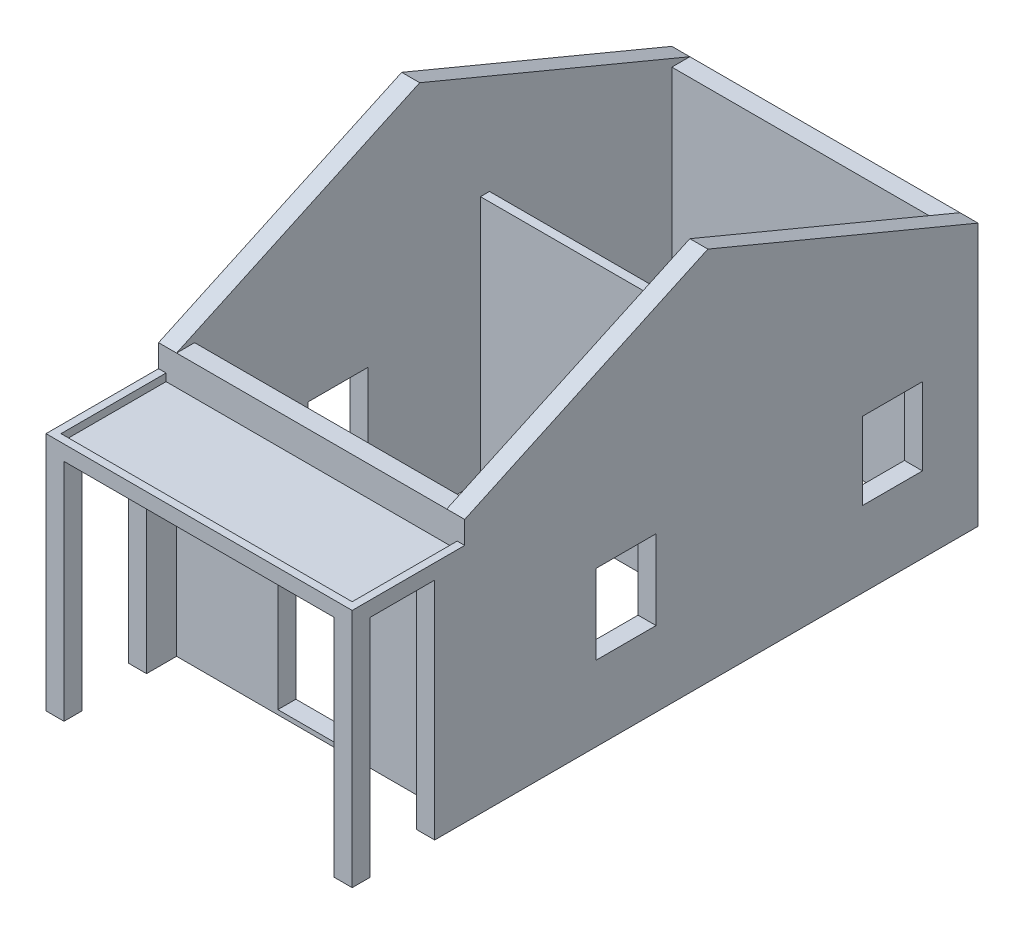
SolidWorks part; units mm, degrees
material "屋面瓦"
ref_plane "前视基准面" through (0, 0, 0) normal (0, 0, 1) x (1, 0, 0)
ref_plane "上视基准面" through (0, 0, 0) normal (0, 1, 0) x (1, 0, 0)
ref_plane "右视基准面" through (0, 0, 0) normal (1, 0, 0) x (0, 0, -1)
sketch "草图1" plane through (0, 0, 0) normal (0, 1, 0) x (1, 0, 0)
  line L1 (0, 0) -> (-3600, 0)
  line L2 (0, 0) -> (0, 6360)
  line L3 (0, 6360) -> (-3600, 6360)
  line L4 (-3600, 0) -> (-3600, 6360)
  point P4 (-1800, 0)
  dimension "D1" = 6360
  dimension "D2" = 3600
extrude "墙" add sketch "草图1" along normal blind 3500 thin thin type one direction wall 240
ref_plane "中间面-宽向" through (-1800, 0, 0) normal (1, 0, 0) x (0, 0, -1)
sketch "草图14" plane through (240, 0, 0) normal (1, 0, 0) x (0, 0, -1)
  line L0 (-240, 3500) -> (3000, 5000)
  line L1 (3000, 5000) -> (6600, 3500)
  line L2 (-240, 0) -> (6600, 0) construction
  line L3 (-240, 3500) -> (6600, 3500)
  dimension "D1" = 5000
  dimension "D2" = 3600
extrude "三角墙" add sketch "草图14" against normal blind 240
mirror "镜向1" about plane through (-1800, 0, 0) normal (1, 0, 0) of "三角墙"
sketch "草图6" plane through (0, 0, 0) normal (0, 1, 0) x (1, 0, 0)
  line L0 (-3600, 3930) -> (0, 3930)
  line L1 (-1800, 3930) -> (-1800, 6360) construction
  line L4 (-3600, 6360) -> (-3600, 6600) construction
  line L5 (0, 0) -> (0, -240) construction
  line L6 (0, 6360) -> (-3600, 6360) construction
  point P10 (-1800, 5145)
  dimension "D1" = 2430
extrude "房墙" add sketch "草图6" along normal blind 3280 thin
ref_plane "房中间面" through (0, 0, -5145) normal (0, 0, 1) x (1, 0, 0)
sketch "草图12" plane through (0, 0, 0) normal (0, 1, 0) x (1, 0, 0)
  line L0 (-1200, 4050) -> (-1200, 3930) construction
  line L1 (0, 3930) -> (-1440, 3930)
  line L2 (0, 3930) -> (0, 4050)
  line L3 (0, 4050) -> (-1440, 4050)
  line L4 (-1440, 3930) -> (-1440, 4050)
  line L5 (-200, 4050) -> (-200, 3930) construction
  dimension "D1" = 200
  dimension "D2" = 120
  dimension "D3" = 240
  dimension "D4" = 1000
extrude "房门框" add sketch "草图12" along normal blind 2520
sketch "草图10" plane through (0, 0, -3810) normal (0, 0, 1) x (1, 0, 0)
  line L0 (-3600, 0) -> (0, 0) construction
  line L1 (-1200, 2050) -> (-200, 2050)
  line L2 (-1200, 2050) -> (-1200, 0)
  line L3 (-1200, 0) -> (-200, 0)
  line L4 (-200, 2050) -> (-200, 0)
  dimension "D1" = 2050
extrude "房门" cut sketch "草图10" against normal up to next
sketch "草图4" plane through (0, 0, -11000) normal (-1, 0, 0) x (0, 0, 1)
  line L0 (11240, 0) -> (4400, 0) construction
  line L1 (5140, 2040) -> (5940, 2040)
  line L2 (5140, 2040) -> (5140, 1010)
  line L3 (5140, 1010) -> (5940, 1010)
  line L4 (5940, 2040) -> (5940, 1010)
  line L6 (4640, 3500) -> (4640, 0) construction
  dimension "D1" = 1030
  dimension "D2" = 800
  dimension "D3" = 1010
  dimension "D4" = 500
extrude "房窗" cut sketch "草图4" against normal through all
sketch "草图13" plane through (0, 0, 240) normal (0, 0, 1) x (1, 0, 0)
  line L0 (0, 3500) -> (0, 0) construction
  line L1 (-2250, 2580) -> (-1250, 2580)
  line L2 (-2250, 2580) -> (-2250, 60)
  line L3 (-2250, 60) -> (-1250, 60)
  line L4 (-1250, 2580) -> (-1250, 60)
  line L5 (-3840, 0) -> (240, 0) construction
  dimension "D1" = 2520
  dimension "D2" = 60
  dimension "D3" = 1000
  dimension "D4" = 1250
extrude "大门" cut sketch "草图13" against normal up to next
sketch "草图15" plane through (240, 0, 0) normal (1, 0, 0) x (0, 0, -1)
  line L0 (-240, 3500) -> (-240, 0) construction
  line L1 (-240, 3100) -> (-1740, 3100)
  line L2 (-240, 3100) -> (-240, 3000)
  line L3 (-240, 3000) -> (-1740, 3000)
  line L4 (-1740, 3100) -> (-1740, 3000)
  line L5 (-240, 0) -> (6600, 0) construction
  dimension "D1" = 100
  dimension "D2" = 3000
  dimension "D3" = 1500
extrude "凸台" add sketch "草图15" against normal up to surface (4080 mm away) up to face at (-3840, 2400, -3144)
sketch "草图16" plane through (0, 3100, 0) normal (0, 1, 0) x (1, 0, 0)
  line L1 (240, -240) -> (0, -240)
  line L2 (240, -240) -> (240, -640)
  line L3 (240, -640) -> (0, -640)
  line L4 (0, -240) -> (0, -640)
  line L5 (240, -1740) -> (0, -1740)
  line L6 (240, -1740) -> (240, -1500)
  line L7 (240, -1500) -> (0, -1500)
  line L8 (0, -1740) -> (0, -1500)
  dimension "D1" = 400
  dimension "D2" = 240
  dimension "D3" = 240
extrude "立柱" add sketch "草图16" against normal up to surface (3100 mm away)
mirror "镜向-立柱" about plane through (-1800, 0, 0) normal (1, 0, 0) of "立柱"
sketch "草图17" plane through (0, 3100, 0) normal (0, 1, 0) x (1, 0, 0)
  line L0 (-3840, -1740) -> (-3840, -240) construction
  line L1 (240, -240) -> (240, -1740) construction
  line L2 (-3840, -1740) -> (-3840, -240)
  line L3 (240, -240) -> (240, -1740)
  line L4 (-3840, -1740) -> (240, -1740) construction
  line L5 (-3840, -1740) -> (240, -1740)
extrude "凸边" add sketch "草图17" along normal blind 100 thin
sketch "草图18" plane through (240, 0, 0) normal (1, 0, 0) x (0, 0, -1)
  line L0 (-640, 0) -> (6600, 0) construction
  line L1 (1510, 2060) -> (2310, 2060)
  line L2 (1510, 2060) -> (1510, 1000)
  line L3 (1510, 1000) -> (2310, 1000)
  line L4 (2310, 2060) -> (2310, 1000)
  line L5 (3810, 3280) -> (3810, 0) construction
  dimension "D1" = 1060
  dimension "D2" = 800
  dimension "D3" = 1000
  dimension "D4" = 1500
extrude "厅窗" cut sketch "草图18" against normal through all
